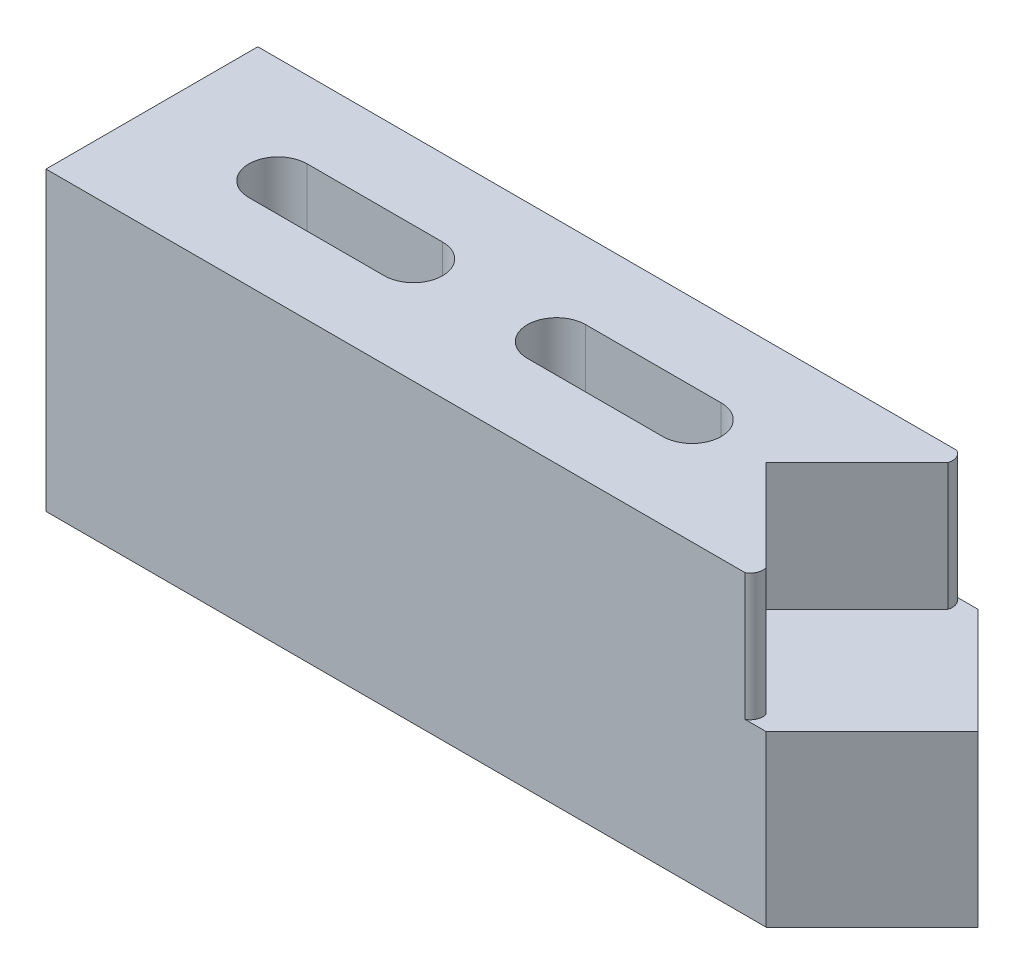
SolidWorks part; units mm, degrees
ref_plane "Front Plane" through (0, 0, 0) normal (0, 0, 1) x (1, 0, 0)
ref_plane "Top Plane" through (0, 0, 0) normal (0, 1, 0) x (1, 0, 0)
ref_plane "Right Plane" through (0, 0, 0) normal (1, 0, 0) x (0, 0, -1)
sketch "Sketch1" plane through (0, 0, 0) normal (0, 0, 1) x (1, 0, 0)
  line L0 (0, 0) -> (43.18, 0)
  line L6 (0, 0) -> (0, 17.78)
  line L10 (0, 17.78) -> (43.18, 17.78)
  line L11 (43.18, 0) -> (43.18, 17.78)
  dimension "D1" = 43.18
  dimension "D2" = 17.78
extrude "Boss-Extrude1" add sketch "Sketch1" against normal blind 12.7
sketch "Sketch3" plane through (0, 17.78, 0) normal (0, 1, 0) x (1, 0, 0)
  line L0 (43.18, 12.7) -> (36.83, 6.35)
  line L1 (36.83, 6.35) -> (43.18, 0)
  line L4 (43.18, 12.7) -> (43.18, 0)
  dimension "D2" = 90
extrude "Cut-Extrude1" cut sketch "Sketch3" against normal blind 7.62
sketch "Sketch4" plane through (0, 17.78, 0) normal (0, 1, 0) x (1, 0, 0)
  line L0 (32.381, 6.35) -> (24.261, 6.35) construction
  line L1 (32.381, 4.6) -> (24.261, 4.6)
  line L2 (32.381, 8.1) -> (24.261, 8.1)
  line L3 (15.681, 6.35) -> (7.561, 6.35) construction
  line L4 (15.681, 4.6) -> (7.561, 4.6)
  line L5 (15.681, 8.1) -> (7.561, 8.1)
  line L6 (43.18, 0) -> (0, 0) construction
  line L7 (0, 12.7) -> (0, 0) construction
  arc A0 (32.381, 4.6) -> (32.381, 8.1) centre (32.381, 6.35) ccw
  arc A1 (24.261, 8.1) -> (24.261, 4.6) centre (24.261, 6.35) ccw
  arc A2 (15.681, 4.6) -> (15.681, 8.1) centre (15.681, 6.35) ccw
  arc A3 (7.561, 8.1) -> (7.561, 4.6) centre (7.561, 6.35) ccw
  point P2 (28.321, 6.35)
  point P7 (11.621, 6.35)
  point P14 (34.131, 6.35)
  point P16 (5.811, 6.35)
  point P18 (17.431, 6.35)
  point P19 (22.511, 6.35)
  dimension "D1" = 1.75
  dimension "D2" = 2.699
  dimension "D3" = 5.811
  dimension "D4" = 6.35
  dimension "D5" = 5.08
extrude "Cut-Extrude2" cut sketch "Sketch4" against normal through all
sketch "Sketch5" plane through (0, 10.16, 0) normal (0, 1, 0) x (1, 0, 0)
  line L0 (43.18, 12.7) -> (49.53, 6.35)
  line L1 (49.53, 6.35) -> (43.18, 0)
  line L2 (43.18, 0) -> (43.18, 12.7) construction
  line L3 (43.18, 0) -> (43.18, 12.7)
  line L4 (36.83, 6.35) -> (43.18, 0) construction
  line L5 (43.18, 12.7) -> (36.83, 6.35) construction
extrude "Boss-Extrude2" add sketch "Sketch5" against normal up to surface (10.16 mm away) up to face at (28.321, 0, -6.35)
sketch "Sketch6" plane through (0, 17.78, 0) normal (0, 1, 0) x (1, 0, 0)
  line L0 (43.18, 12.7) -> (0, 12.7) construction
  line L1 (43.18, 12.7) -> (36.83, 6.35) construction
  line L2 (41.91, 12.7) -> (43.18, 12.7)
  line L3 (43.18, 12.7) -> (42.282, 11.802)
  line L4 (36.83, 6.35) -> (49.2302, 6.35) construction
  line L5 (41.91, 0) -> (43.18, 0)
  line L6 (43.18, 0) -> (42.282, 0.898)
  arc A0 (41.91, 12.7) -> (42.282, 11.802) centre (41.5538, 12.0264) cw
  arc A1 (41.91, 0) -> (42.282, 0.898) centre (41.5538, 0.6736) ccw
  dimension "D3" = 0.762
  dimension "D1" = 1.27
  dimension "D2" = 1.27
extrude "Cut-Extrude3" cut sketch "Sketch6" against normal up to surface (7.62 mm away) up to face at (43.18, 10.16, -6.35)
